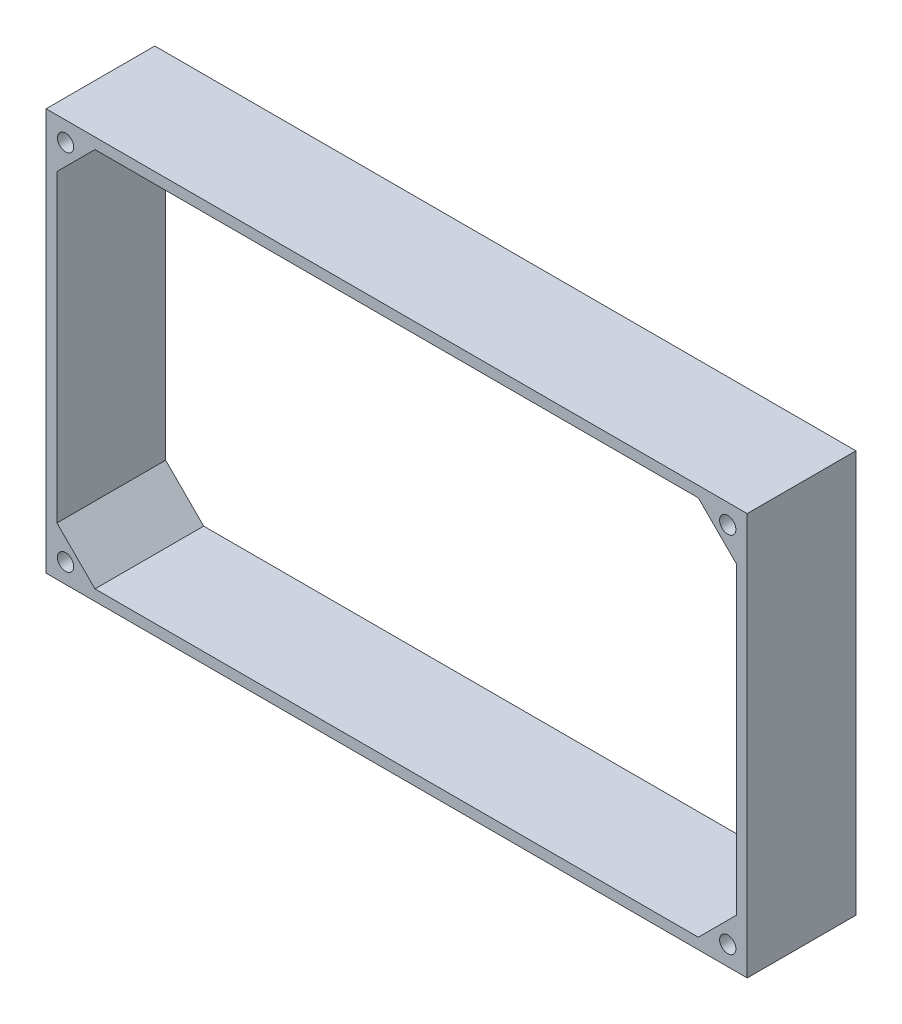
SolidWorks part; units mm, degrees
ref_plane "Plan de face" through (0, 0, 0) normal (0, 0, 1) x (1, 0, 0)
ref_plane "Plan de dessus" through (0, 0, 0) normal (0, 1, 0) x (1, 0, 0)
ref_plane "Plan de droite" through (0, 0, 0) normal (1, 0, 0) x (0, 0, -1)
sketch "Esquisse1" plane through (0, 0, 0) normal (0, 0, 1) x (1, 0, 0)
  line L1 (-125, -70) -> (-111, -70) construction
  line L2 (0, -70.95) -> (0, 70.95) construction
  line L3 (-111, 70) -> (111, 70)
  line L4 (131.45, 0) -> (-131.45, 0) construction
  line L5 (-125, 70) -> (-111, 70) construction
  line L6 (-129, -74) -> (129, -74)
  line L7 (129, 74) -> (129, -74)
  line L8 (-129, 74) -> (129, 74)
  line L9 (-129, 74) -> (-129, -74)
  line L10 (-115, 60) -> (-115, -60) construction
  line L11 (-115, -60) -> (115, -60) construction
  line L12 (115, 60) -> (115, -60) construction
  line L13 (-115, 60) -> (115, 60) construction
  line L14 (-111, 70) -> (-125, 56)
  line L15 (-111, -70) -> (-125, -56)
  line L16 (111, 70) -> (125, 56)
  line L17 (111, -70) -> (125, -56)
  line L18 (-129, 74) -> (-118, 63) construction
  line L19 (-129, 74) -> (-118, 63) construction
  line L20 (-125, 56) -> (-125, -56)
  line L21 (-125, 70) -> (-125, -70) construction
  line L22 (125, 56) -> (125, -56)
  line L23 (125, 70) -> (125, -70) construction
  line L25 (-125, 70) -> (125, 70) construction
  line L27 (111, -70) -> (125, -70) construction
  line L28 (-125, -70) -> (125, -70) construction
  line L29 (-111, -70) -> (111, -70)
  circle A0 centre (-121.8321, 66.8321) radius 3
  circle A1 centre (-121.8321, -66.8321) radius 3
  circle A2 centre (121.8321, -66.8321) radius 3
  circle A3 centre (121.8321, 66.8321) radius 3
  point P16 (-125, 56)
  point P17 (-111, 70)
  point P31 (-121.2701, 65.2229)
  point P32 (-123.4302, 62.4702)
  point P33 (-121.2128, 66.064)
  point P34 (-121.8321, 66.8321)
  point P35 (-125, 56.4634)
  point P36 (-135.6906, 81.996)
  point P37 (93.5721, -48.4529)
  point P40 (-125, -57.5745)
  point P44 (-151.9446, -47.4533)
  dimension "D8" = 0
  dimension "D1" = 140
  dimension "D2" = 250
  dimension "D4" = 14
  dimension "D5" = 120
  dimension "D6" = 230
  dimension "D7" = 14
  dimension "D3" = 4
extrude "Boss.-Extru.2" add sketch "Esquisse1" along normal blind 40 contours L8 L9 L6 L7 A1 A0 L29 L15 L20 L14 L3 L16 L22 L17 A2 A3
